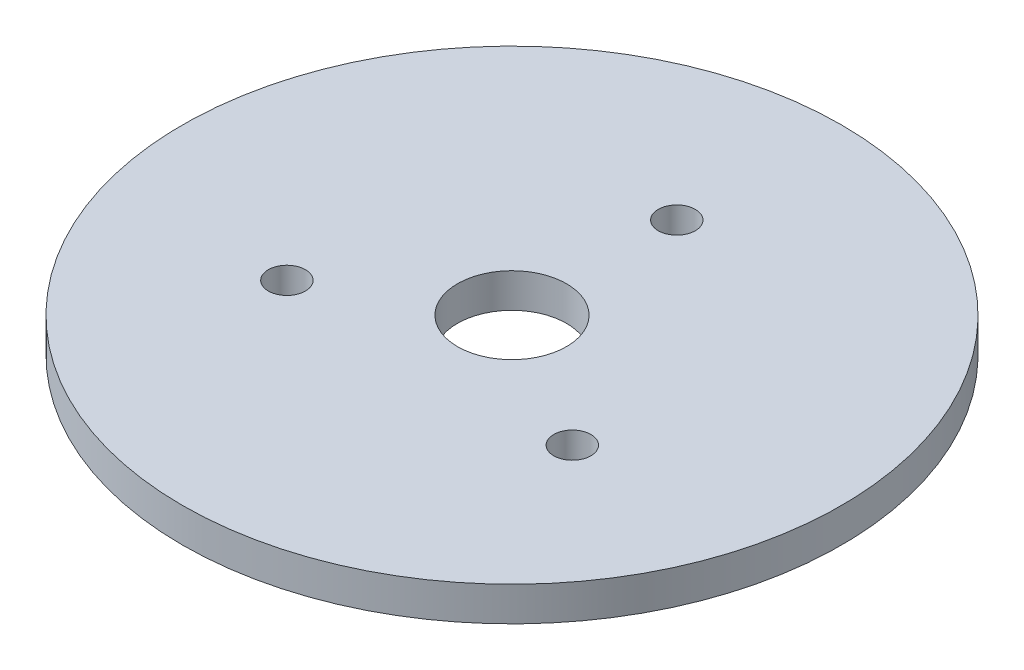
SolidWorks part; units mm, degrees
ref_plane "Front Plane" through (0, 0, 0) normal (0, 0, 1) x (1, 0, 0)
ref_plane "Top Plane" through (0, 0, 0) normal (0, 1, 0) x (1, 0, 0)
ref_plane "Right Plane" through (0, 0, 0) normal (1, 0, 0) x (0, 0, -1)
sketch "Sketch1" plane through (0, 0, 0) normal (0, 1, 0) x (1, 0, 0)
  line L0 (0, 0) -> (0, 23.9927) construction
  circle A0 centre (0, 0) radius 23.9927
  circle A1 centre (0, 11.9963) radius 1.35
  circle A2 centre (10.3891, -5.9982) radius 1.35
  circle A3 centre (-10.3891, -5.9982) radius 1.35
  point P13 (0, 0)
  dimension "D1" = 47.9854
  dimension "D2" = 2.7
  dimension "D4" = 11.9963
  dimension "D3" = 3
extrude "Boss-Extrude1" add sketch "Sketch1" along normal blind 2.5
sketch "Sketch3" plane through (0, 2.5, 0) normal (0, 1, 0) x (1, 0, 0)
  line L0 (5.7358, 8.1915) -> (8.6036, 12.2873)
  line L1 (0, 0) -> (28.6334, 16.5315) construction
  line L2 (0, 0) -> (0, 25.5344) construction
  line L3 (9.9619, 0.8716) -> (14.9429, 1.3073)
  line L4 (4.2262, -9.0631) -> (6.3393, -13.5946)
  line L5 (-4.2262, -9.0631) -> (-6.3393, -13.5946)
  line L6 (-9.9619, 0.8716) -> (-14.9429, 1.3073)
  line L7 (-5.7358, 8.1915) -> (-8.6036, 12.2873)
  arc A0 (9.9619, 0.8716) -> (5.7358, 8.1915) centre (0, 0) ccw
  arc A1 (14.9429, 1.3073) -> (8.6036, 12.2873) centre (0, 0) ccw
  arc A2 (-6.3393, -13.5946) -> (6.3393, -13.5946) centre (0, 0) ccw
  arc A3 (-4.2262, -9.0631) -> (4.2262, -9.0631) centre (0, 0) ccw
  arc A4 (-8.6036, 12.2873) -> (-14.9429, 1.3073) centre (0, 0) ccw
  arc A5 (-5.7358, 8.1915) -> (-9.9619, 0.8716) centre (0, 0) ccw
  point P19 (0, 0)
  dimension "D1" = 30
  dimension "D2" = 20
  dimension "D3" = 60
  dimension "D4" = 25
extrude "Cut-Extrude2" [suppressed] cut sketch "Sketch3" against normal blind 10
sketch "Sketch4" plane through (0, 2.5, 0) normal (0, 1, 0) x (1, 0, 0)
  circle A0 centre (0, 0) radius 3.9688
  dimension "D1" = 7.9375
extrude "Cut-Extrude3" cut sketch "Sketch4" against normal through all
